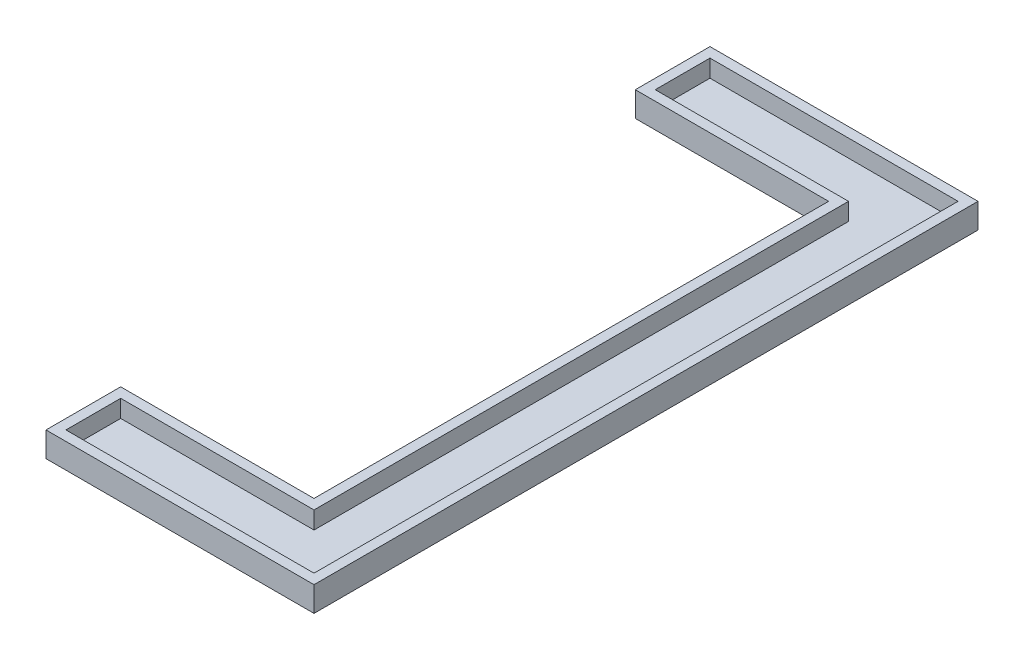
SolidWorks part; units mm, degrees
ref_plane "Front Plane" through (0, 0, 0) normal (0, 0, 1) x (1, 0, 0)
ref_plane "Top Plane" through (0, 0, 0) normal (0, 1, 0) x (1, 0, 0)
ref_plane "Right Plane" through (0, 0, 0) normal (1, 0, 0) x (0, 0, -1)
sketch "Sketch1" plane through (0, 0, 0) normal (0, 1, 0) x (1, 0, 0)
  line L1 (0, 106.68) -> (43.06, 106.68)
  line L2 (0, 106.68) -> (0, 94.68)
  line L3 (0, 94.68) -> (31.06, 94.68)
  line L6 (43.06, 106.68) -> (43.06, 0)
  line L8 (31.06, 94.68) -> (31.06, 12)
  line L9 (43.06, 0) -> (0, 0)
  line L11 (31.06, 12) -> (0, 12)
  line L12 (0, 0) -> (0, 12)
  dimension "D1" = 12
  dimension "D2" = 12
  dimension "D3" = 12
  dimension "D4" = 43.06
  dimension "D5" = 106.68
extrude "Boss-Extrude1" add sketch "Sketch1" along normal blind 4
sketch "Sketch2" plane through (0, 4, 0) normal (0, 1, 0) x (1, 0, 0)
  line L16 (1.6, 105.08) -> (1.6, 96.28)
  line L17 (1.6, 96.28) -> (32.66, 96.28)
  line L18 (32.66, 96.28) -> (32.66, 10.4)
  line L19 (32.66, 10.4) -> (1.6, 10.4)
  line L20 (1.6, 10.4) -> (1.6, 1.6)
  line L21 (1.6, 1.6) -> (41.46, 1.6)
  line L22 (41.46, 1.6) -> (41.46, 105.08)
  line L23 (41.46, 105.08) -> (1.6, 105.08)
  line L24 (1.6, 105.08) -> (1.6, 96.28)
  line L25 (1.6, 96.28) -> (32.66, 96.28)
  line L26 (32.66, 96.28) -> (32.66, 10.4)
  line L27 (32.66, 10.4) -> (1.6, 10.4)
  line L28 (1.6, 10.4) -> (1.6, 1.6)
  line L29 (1.6, 1.6) -> (41.46, 1.6)
  line L30 (41.46, 1.6) -> (41.46, 105.08)
  line L31 (41.46, 105.08) -> (1.6, 105.08)
  dimension "D1" = 1.6
extrude "Cut-Extrude1" cut sketch "Sketch2" against normal blind 2.8
